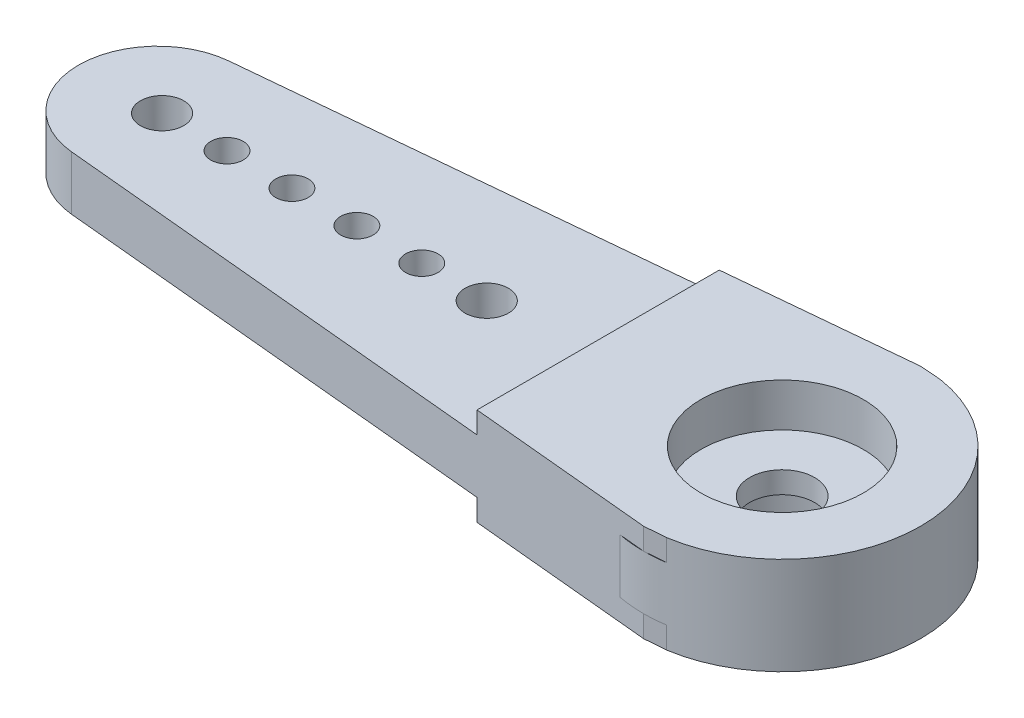
SolidWorks part; units mm, degrees
ref_plane "Front Plane" through (0, 0, 0) normal (0, 0, 1) x (1, 0, 0)
ref_plane "Top Plane" through (0, 0, 0) normal (0, 1, 0) x (1, 0, 0)
ref_plane "Right Plane" through (0, 0, 0) normal (1, 0, 0) x (0, 0, -1)
sketch "ｽｹｯﾁ1" plane through (0, 0, 0) normal (0, 1, 0) x (1, 0, 0)
  line L0 (28.85, 0) -> (0, 0)
  line L1 (28.85, 6.4) -> (-0.3443, 3.6337)
  line L2 (28.85, -6.4) -> (-0.3443, -3.6337)
  circle A0 centre (28.85, 0) radius 6.4
  circle A2 centre (0, 0) radius 3.65
  dimension "D2" = 12.8
  dimension "D4" = 7.3
extrude "ﾎﾞｽ - 押し出し1" add sketch "ｽｹｯﾁ1" along normal blind 2.5
sketch "ｽｹｯﾁ2" plane through (0, 2.5, 0) normal (0, 1, 0) x (1, 0, 0)
  line L0 (20.35, 5.5946) -> (20.35, -5.5946)
  line L1 (27.6479, 6.2861) -> (-0.3443, 3.6337) construction
  line L2 (27.6479, -6.2861) -> (-0.3443, -3.6337) construction
  line L3 (37.35, -5.7408) -> (37.35, 5.7408)
  line L4 (28.85, -6.4) -> (58.0209, -4.1376) construction
  line L5 (28.85, 6.4) -> (58.0209, 4.1376) construction
  line L6 (20.35, 5.5946) -> (28.85, 6.4)
  line L7 (28.85, 6.4) -> (37.35, 5.7408)
  line L8 (37.35, -5.7408) -> (36.4541, -5.8102)
  line L9 (28.85, -6.4) -> (20.35, -5.5946)
  line L10 (37.35, -5.7408) -> (28.85, -6.4)
  dimension "D1" = 8.5
  dimension "D2" = 8.5
extrude "ﾎﾞｽ - 押し出し2" add sketch "ｽｹｯﾁ2" along normal blind 1 and the other way blind 3.5
sketch "ｽｹｯﾁ4" plane through (0, 3.5, 0) normal (0, 1, 0) x (1, 0, 0)
  circle A0 centre (28.85, 0) radius 1.5
  dimension "D1" = 3
extrude "ｶｯﾄ - 押し出し1" cut sketch "ｽｹｯﾁ4" against normal blind 14.5
sketch "ｽｹｯﾁ7" plane through (0, 2.5, 0) normal (0, 1, 0) x (1, 0, 0)
  line L0 (0.2048, 0) -> (15.2048, 0) construction
  circle A0 centre (57.7, 0) radius 1
  circle A1 centre (15.2048, 0) radius 1
  circle A2 centre (54.7, 0) radius 1
  circle A3 centre (51.7, 0) radius 1
  circle A4 centre (48.7, 0) radius 1
  circle A5 centre (45.7, 0) radius 1
  circle A7 centre (12.2048, 0) radius 0.75
  circle A8 centre (9.2048, 0) radius 0.75
  circle A9 centre (6.2048, 0) radius 0.75
  circle A10 centre (3.2048, 0) radius 0.75
  circle A11 centre (0.2048, 0) radius 1
  dimension "D1" = 2
  dimension "D3" = 2
  dimension "D4" = 1.5
  dimension "D5" = 1.5
  dimension "D6" = 1.5
  dimension "D7" = 1.5
  dimension "D8" = 2
  dimension "D9" = 3
  dimension "D10" = 3
  dimension "D11" = 3
  dimension "D12" = 3
  dimension "D13" = 3
  dimension "D2" = 5
extrude "ｶｯﾄ - 押し出し4" cut sketch "ｽｹｯﾁ7" against normal blind 3
sketch "ｽｹｯﾁ8" plane through (0, -1, 0) normal (0, -1, 0) x (-1, 0, 0)
  circle A0 centre (-28.85, 0) radius 4.75
  dimension "D1" = 9.5
extrude "ﾎﾞｽ - 押し出し3" add sketch "ｽｹｯﾁ8" along normal blind 1.5 draft 23
sketch "ｽｹｯﾁ9" plane through (0, -2.5, 0) normal (0, -1, 0) x (-1, 0, 0)
  circle A0 centre (-28.85, 0) radius 3.25
  dimension "D1" = 6.5
extrude "ｶｯﾄ - 押し出し5" cut sketch "ｽｹｯﾁ9" against normal blind 3
sketch "ｽｹｯﾁ10" plane through (0, 3.5, 0) normal (0, 1, 0) x (1, 0, 0)
  circle A0 centre (28.85, 0) radius 3.75
  circle A1 centre (28.85, 0) radius 1.5 construction
  dimension "D1" = 0
  dimension "D2" = 7.5
extrude "ｶｯﾄ - 押し出し6" cut sketch "ｽｹｯﾁ10" against normal blind 2
